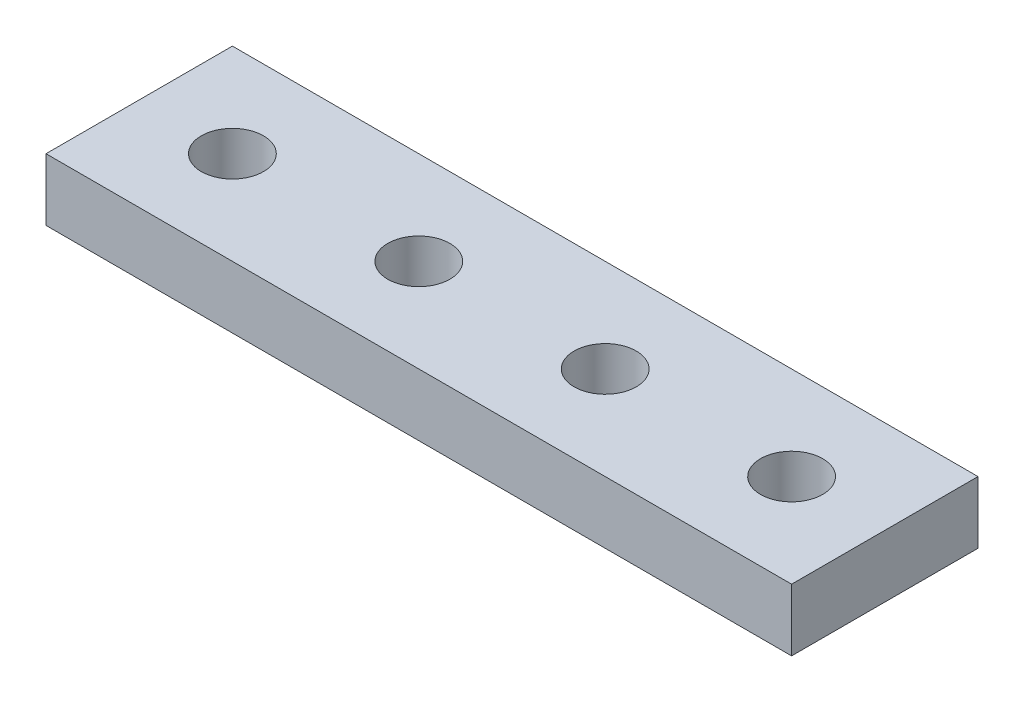
SolidWorks part; units mm, degrees
ref_plane "Front Plane" through (0, 0, 0) normal (0, 0, 1) x (1, 0, 0)
ref_plane "Top Plane" through (0, 0, 0) normal (0, 1, 0) x (1, 0, 0)
ref_plane "Right Plane" through (0, 0, 0) normal (1, 0, 0) x (0, 0, -1)
sketch "Sketch1" plane through (0, 0, 0) normal (0, 1, 0) x (1, 0, 0)
  line L1 (-60, -15) -> (60, -15)
  line L2 (-60, -15) -> (-60, 15)
  line L3 (-60, 15) -> (60, 15)
  line L4 (60, -15) -> (60, 15)
  line L5 (-60, -15) -> (60, 15) construction
  line L6 (-60, 15) -> (60, -15) construction
  point P0 (0, 0)
  dimension "D1" = 120
  dimension "D2" = 30
extrude "Boss-Extrude1" add sketch "Sketch1" along normal blind 10
sketch "Sketch3" plane through (0, 10, 0) normal (0, 1, 0) x (1, 0, 0)
  line L0 (-60, 15) -> (-60, -15) construction
  circle A0 centre (-45, 0) radius 5
  circle A1 centre (-15, 0) radius 5
  circle A2 centre (15, 0) radius 5
  circle A3 centre (45, 0) radius 5
  dimension "D1" = 10
  dimension "D2" = 15
  dimension "D3" = 4
extrude "Cut-Extrude1" cut sketch "Sketch3" against normal through all
